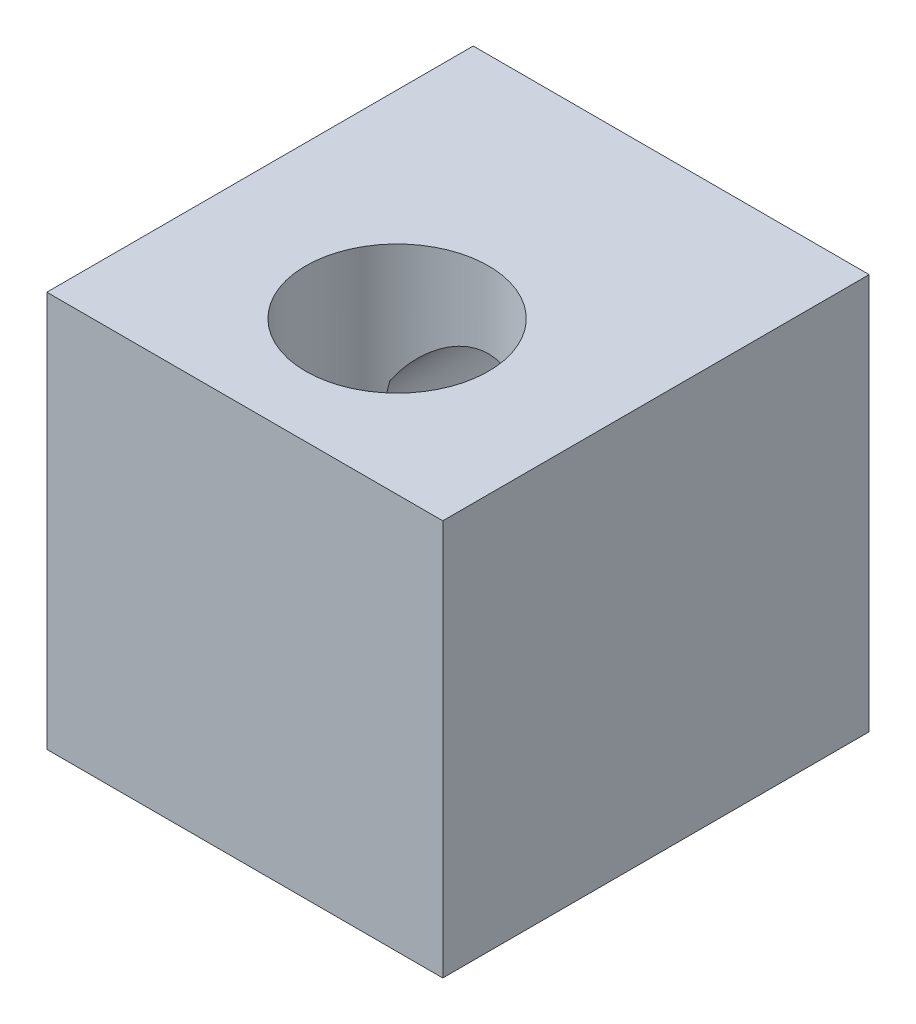
SolidWorks part; units mm, degrees
ref_plane "Front Plane" through (0, 0, 0) normal (0, 0, 1) x (1, 0, 0)
ref_plane "Top Plane" through (0, 0, 0) normal (0, 1, 0) x (1, 0, 0)
ref_plane "Right Plane" through (0, 0, 0) normal (1, 0, 0) x (0, 0, -1)
sketch "Sketch1" plane through (0, 0, 0) normal (0, 0, 1) x (1, 0, 0)
  line L0 (-6.5, -6.5) -> (6.5, -6.5)
  line L1 (-6.5, -6.5) -> (-6.5, 6.5)
  line L2 (6.5, -6.5) -> (6.5, 6.5)
  line L3 (-6.5, 6.5) -> (6.5, 6.5)
  line L4 (6.5, 0) -> (-6.5, 0) construction
  line L5 (0, -6.5) -> (0, 6.5) construction
  point P1 (0, 0)
extrude "Boss-Extrude1" add sketch "Sketch1" along normal blind 14
sketch "Sketch2" plane through (0, 6.5, 0) normal (0, 1, 0) x (1, 0, 0)
  line L1 (6.5, -14) -> (-6.5, -14) construction
  line L2 (-6.5, -14) -> (-6.5, 0) construction
  circle A0 centre (0, -9) radius 3
  dimension "D1" = 5
  dimension "D2" = 6.5
hole_wizard "Ø6.0mm Dowel Hole1" positions "Sketch5" profile "Sketch6" hole size "Ø6.0" standard "ANSI Metric" end condition up to next
sketch "Sketch5" plane through (0, 6.5, 0) normal (0, 1, 0) x (1, 0, 0)
  line L0 (6.5, -14) -> (6.5, 0) construction
  line L1 (6.5, -14) -> (-6.5, -14) construction
  point P0 (0, -9)
  dimension "D1" = 6.5
  dimension "D2" = 5
sketch "Sketch6" plane through (0, 6.5, 9) normal (1, 0, 0) x (0, 0, 1)
  line L0 (0, 0) -> (0, 13)
  line L1 (0, 13) -> (3, 13)
  line L2 (3, 13) -> (3, 0)
  line L5 (3, 0) -> (0, 0)
  line L11 (0, -6.35) -> (0, 107.95) construction
  dimension "Thru Hole Dia." = 6
  dimension "Thru Hole Depth" = 13
hole_wizard "M6x1.0 Tapped Hole6" positions "Sketch9" profile "Sketch10" tap size "M6x1.0" standard "ANSI Metric"
sketch "Sketch9" plane through (0, 0, 0) normal (0, 0, -1) x (-1, 0, 0)
  line L0 (6.5, 6.5) -> (6.5, -6.5) construction
  line L1 (-6.5, 6.5) -> (6.5, 6.5) construction
  point P0 (0, 1.5)
  dimension "D1" = 6.5
  dimension "D2" = 5
sketch "Sketch10" plane through (0, 1.5, 0) normal (1, 0, 0) x (0, 1, 0)
  line L0 (0, 0) -> (0, 8.5022)
  line L1 (0, 8.5022) -> (2.5, 7)
  line L2 (2.5, 7) -> (2.5, 0)
  line L5 (2.5, 0) -> (0, 0)
  line L10 (0, 8.5022) -> (-2.5, 7) construction
  line L11 (0, -6.35) -> (0, 107.95) construction
  dimension "Tap Drill Dia." = 5
  dimension "Tap Drill Depth" = 7
  dimension "Drill Angle" = 118
cosmetic thread "Hole Thread2" parameters "D1"=12, "D2"=6
